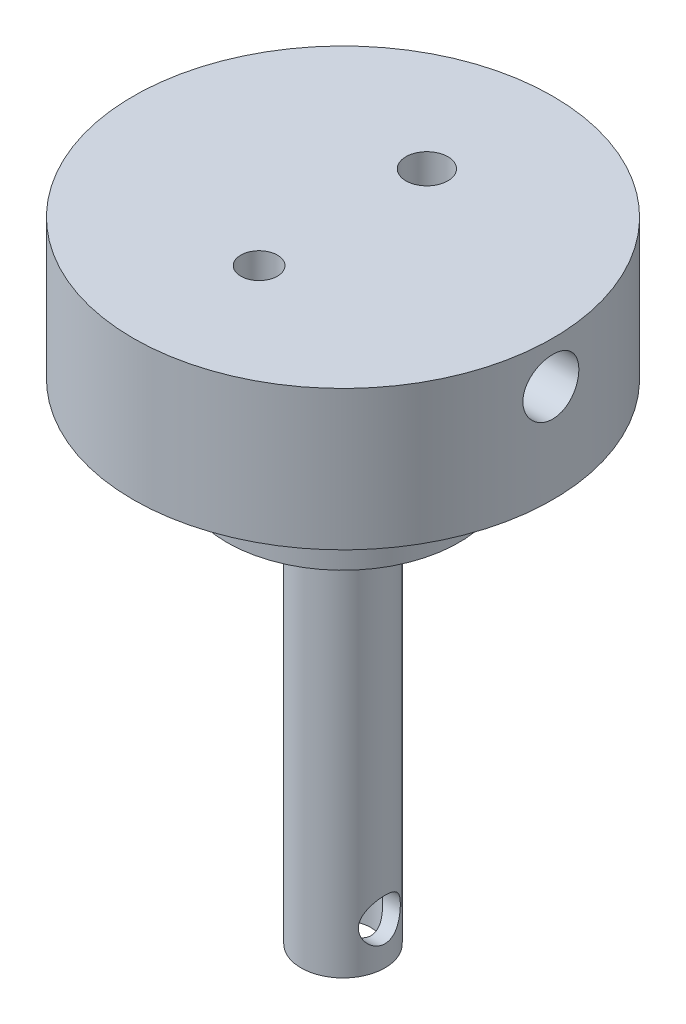
SolidWorks part; units mm, degrees
ref_plane "Front Plane" through (0, 0, 0) normal (0, 0, 1) x (1, 0, 0)
ref_plane "Top Plane" through (0, 0, 0) normal (0, 1, 0) x (1, 0, 0)
ref_plane "Right Plane" through (0, 0, 0) normal (1, 0, 0) x (0, 0, -1)
sketch "Sketch1" plane through (0, 0, 0) normal (0, 1, 0) x (1, 0, 0)
  circle A0 centre (0, 0) radius 7.5
extrude "Boss-Extrude1" add sketch "Sketch1" along normal blind 5
sketch "Sketch5" plane through (0, 0, 0) normal (0, 0, 1) x (1, 0, 0)
  line L0 (0, 0) -> (0, 0.5)
  line L1 (3, 3.5) -> (7.5, 3.5)
  line L2 (7.5, 0) -> (7.5, 5) construction
  arc A0 (0, 0.5) -> (3, 3.5) centre (3, 0.5) cw
  point P8 (0, 0)
  point P9 (0, 0)
  dimension "D1" = 3
sketch "Sketch6" plane through (0, 0, 0) normal (0, -1, 0) x (-1, 0, 0)
  circle A0 centre (0, 0) radius 1
sweep "Cut-Sweep2" cut profiles "Sketch6" path "Sketch5"
ref_plane "Plane1" through (10, 0, 0) normal (1, 0, 0) x (0, 0, -1)
sketch "Sketch12" plane through (0, 0, 0) normal (0, -1, 0) x (-1, 0, 0)
  circle A0 centre (0, 0) radius 4.15
extrude "Boss-Extrude2" add sketch "Sketch12" along normal blind 3
sketch "Sketch13" plane through (0, -3, 0) normal (0, -1, 0) x (1, 0, 0)
  circle A0 centre (0, 0) radius 1.5
extrude "Boss-Extrude3" add sketch "Sketch13" along normal blind 14.5
sketch "Sketch21" plane through (0, -17.5, 0) normal (0, -1, 0) x (-1, 0, 0)
  circle A0 centre (0, 0) radius 1
extrude "Cut-Extrude5" cut sketch "Sketch21" against normal up to next
sketch "Sketch22" plane through (10, 0, 0) normal (1, 0, 0) x (0, 0, -1)
  circle A0 centre (0, -16) radius 0.75
extrude "Cut-Extrude6" cut sketch "Sketch22" against normal through all
sketch "Sketch23" plane through (0, -3, 0) normal (0, -1, 0) x (1, 0, 0)
  circle A0 centre (0, 3) radius 0.6549
  circle A1 centre (0, -3) radius 0.75
extrude "Cut-Extrude7" cut sketch "Sketch23" against normal blind 10
